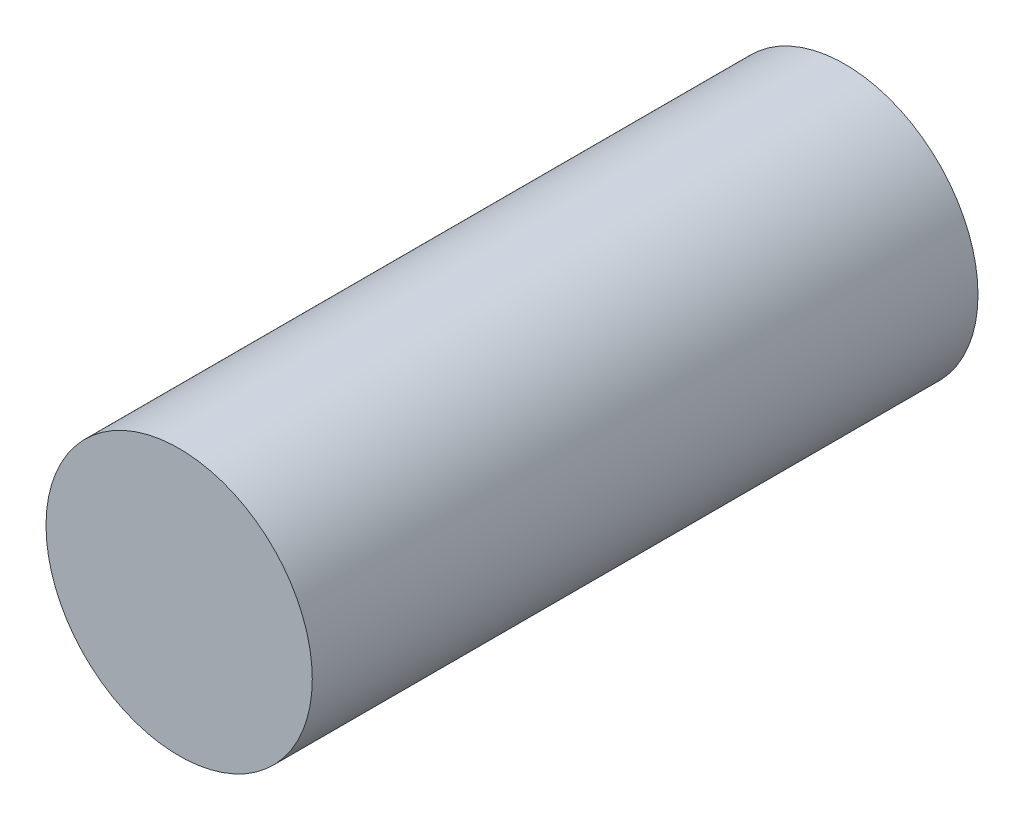
SolidWorks part; units mm, degrees
ref_plane "Front Plane" through (0, 0, 0) normal (0, 0, 1) x (1, 0, 0)
ref_plane "Top Plane" through (0, 0, 0) normal (0, 1, 0) x (1, 0, 0)
ref_plane "Right Plane" through (0, 0, 0) normal (1, 0, 0) x (0, 0, -1)
sketch "Sketch1" plane through (0, 0, 0) normal (0, 0, 1) x (1, 0, 0)
  circle A0 centre (0, 0) radius 4
extrude "Boss-Extrude1" add sketch "Sketch1" along normal blind 20
